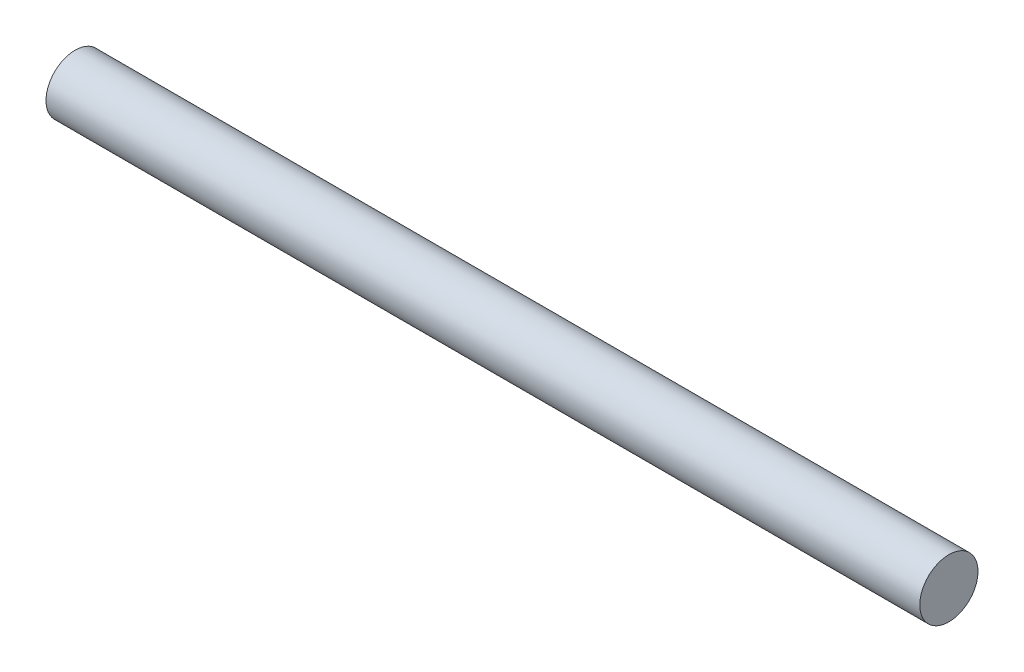
SolidWorks part; units mm, degrees
ref_plane "Front Plane" through (0, 0, 0) normal (0, 0, 1) x (1, 0, 0)
ref_plane "Top Plane" through (0, 0, 0) normal (0, 1, 0) x (1, 0, 0)
ref_plane "Right Plane" through (0, 0, 0) normal (1, 0, 0) x (0, 0, -1)
sketch "Sketch1" plane through (0, 0, 0) normal (0, 0, 1) x (1, 0, 0)
  line L0 (0, 0) -> (-75, 0)
  line L5 (-75, 0) -> (-75, 5)
  line L6 (-75, 5) -> (75, 5)
  line L7 (75, 5) -> (75, 0)
  line L8 (75, 0) -> (0, 0)
  line L9 (-80, 0) -> (-75, 0)
  line L10 (80, 0) -> (75, 0)
  dimension "D3" = 5
  dimension "D1" = 75
  dimension "D2" = 75
revolve "Revolve4" add sketch "Sketch1" angle 360 about L0
